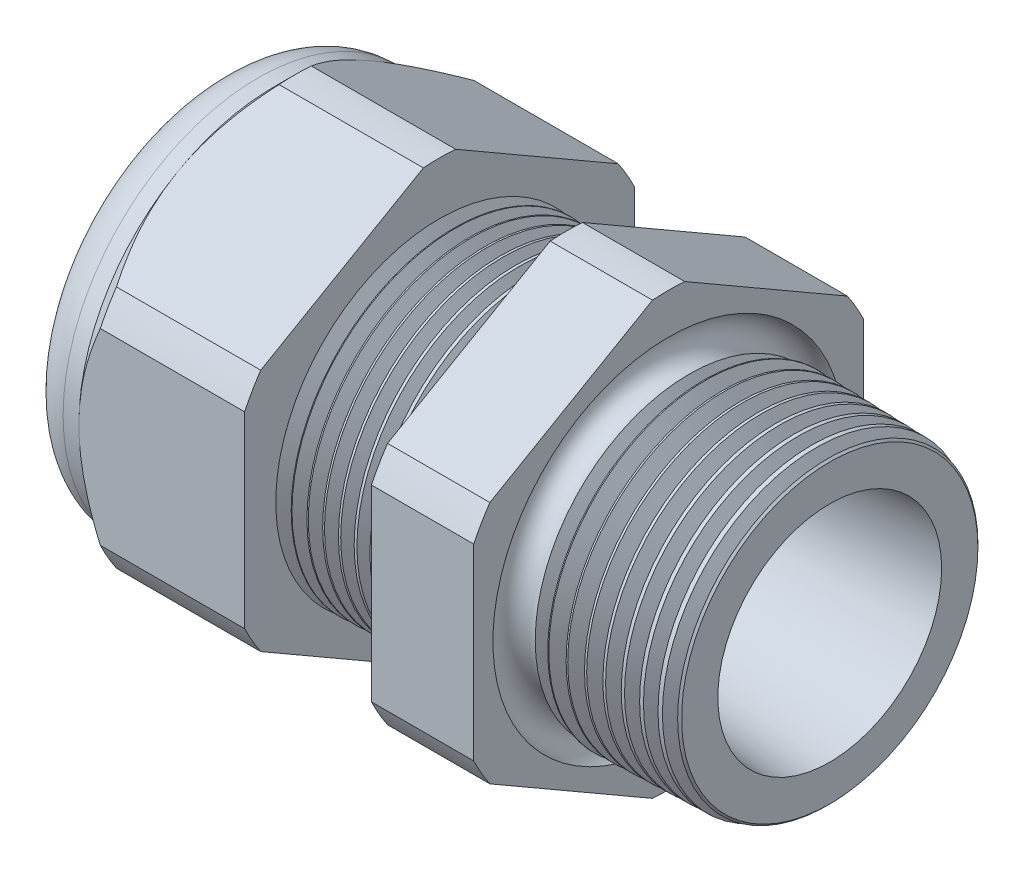
SolidWorks part; units mm, degrees
ref_plane "Front Plane" through (0, 0, 0) normal (0, 0, 1) x (1, 0, 0)
ref_plane "Top Plane" through (0, 0, 0) normal (0, 1, 0) x (1, 0, 0)
ref_plane "Right Plane" through (0, 0, 0) normal (1, 0, 0) x (0, 0, -1)
sketch "Sketch10" plane through (0, 0, 0) normal (0, 0, 1) x (1, 0, 0)
  line L0 (0, 0) -> (-115.3565, 0) construction
  line L1 (-29.972, 3.937) -> (-19.072, 3.937)
  line L2 (0, 5.4696) -> (0, 7.5016)
  line L3 (-7.874, 7.7078) -> (0, 7.5016)
  line L4 (-7.874, 19.05) -> (-7.874, 7.7078)
  line L5 (-7.874, 19.05) -> (-12.874, 19.05)
  line L6 (-12.874, 19.05) -> (-12.874, 7.8387)
  line L7 (-19.072, 8.001) -> (-12.874, 7.8387)
  line L8 (-19.072, 8.001) -> (-19.072, 19.05)
  line L9 (-19.072, 19.05) -> (-27.172, 19.05)
  line L10 (-27.172, 19.05) -> (-27.172, 9.525)
  line L11 (-27.172, 9.525) -> (-29.972, 9.525)
  line L12 (-29.972, 9.525) -> (-29.972, 3.937)
  line L13 (-19.072, 3.937) -> (0, 5.4696)
  dimension "D1" = 29.972
  dimension "D2" = 7.874
  dimension "D3" = 1.5
  dimension "D4" = 2.032
  dimension "A" = 16.002
  dimension "D6" = 19.05
  dimension "D8" = 38.1
  dimension "D9" = 2.8
  dimension "D10" = 8.1
  dimension "D11" = 5
  dimension "D" = 7.874
revolve "Revolve2" add sketch "Sketch10" angle 360 about L0
sketch "Sketch12" plane through (-27.172, 0, 0) normal (-1, 0, 0) x (0, 0, 1)
  line L1 (-0.7885, 10.5433) -> (-8.7365, 5.9545)
  line L2 (-9.525, 4.5888) -> (-9.525, -4.5888)
  line L3 (-8.7365, -5.9545) -> (-0.7885, -10.5433)
  line L4 (0.7885, -10.5433) -> (8.7365, -5.9545)
  line L5 (9.525, -4.5888) -> (9.525, 4.5888)
  line L6 (8.7365, 5.9545) -> (0.7885, 10.5433)
  circle A0 centre (0, 0) radius 9.525 construction
  arc A1 (0.7885, 10.5433) -> (-0.7885, 10.5433) centre (0, 0) ccw
  arc A2 (-8.7365, 5.9545) -> (-9.525, 4.5888) centre (0, 0) ccw
  arc A3 (-9.525, -4.5888) -> (-8.7365, -5.9545) centre (0, 0) ccw
  arc A4 (-0.7885, -10.5433) -> (0.7885, -10.5433) centre (0, 0) ccw
  arc A5 (8.7365, -5.9545) -> (9.525, -4.5888) centre (0, 0) ccw
  arc A6 (9.525, 4.5888) -> (8.7365, 5.9545) centre (0, 0) ccw
  dimension "D2" = 21.1455
  dimension "D1" = 19.05
extrude "Cut-Extrude2" cut sketch "Sketch12" against normal through all flip side to cut
fillet "Fillet4" radius 2.032 1 edges at (-29.972, 0, -9.525)
sketch "Sketch19" plane through (-27.172, 0, 0) normal (-1, 0, 0) x (0, 0, 1)
  line L0 (9.525, 0) -> (9.525, 4.5888) construction
  circle A0 centre (0, 0) radius 9.525
extrude "Cut-Extrude3" cut sketch "Sketch19" against normal blind 2 draft 45 flip side to cut
chamfer "Chamfer1" distance 0.254 angle 45 1 edges at (0, 0, -7.5016)
sketch "Sketch21" plane through (-29.972, 0, 0) normal (-1, 0, 0) x (0, 0, 1)
  circle A0 centre (0, 0) radius 3.937
  circle A2 centre (0, 0) radius 3.937 construction
extrude "plug" add sketch "Sketch21" against normal blind 3.81 separate body
sketch "Sketch22" plane through (-29.972, 0, 0) normal (-1, 0, 0) x (0, 0, 1)
  circle A0 centre (0, 0) radius 3.683
  circle A1 centre (0, 0) radius 3.937 construction
  dimension "D1" = 0.254
extrude "Cut-Extrude4" cut sketch "Sketch22" against normal blind 0.508
sketch "Sketch27" plane through (-29.464, 0, 0) normal (-1, 0, 0) x (0, 0, 1)
  line L0 (-4.3624, 0) -> (4.3624, 0) construction
  circle A0 centre (-2.1529, 0) radius 1.524
  circle A1 centre (0, 0) radius 3.683 construction
  dimension "D1" = 0.0061
  dimension "holedia" = 3.048
extrude "plugholes" cut sketch "Sketch27" against normal through all
pattern_circular "CirPattern1" count 2 over 360 about axis through (0, 0, 0) along (1, 0, 0) of "plugholes"
sketch "Sketch28" [suppressed] plane through (-29.464, 0, 0) normal (-1, 0, 0) x (0, 0, 1)
  circle A0 centre (0, 0) radius 0.762
  dimension "midholedia" = 3.048
extrude "midhole" [suppressed] cut sketch "Sketch28" against normal through all
sketch "Sketch29" plane through (0, 0, 0) normal (0, 0, 1) x (1, 0, 0)
  line L0 (-19.072, 8.001) -> (-18.339, 7.9818)
  line L1 (-12.874, 7.8387) -> (-19.072, 8.001) construction
  line L2 (-18.339, 7.9818) -> (-18.7221, 7.3566)
  line L3 (-18.7221, 7.3566) -> (-19.072, 8.001)
  dimension "D1" = 60
  dimension "D2" = 60
  dimension "D3" = 0.635
revolve "Cut-Revolve1" cut sketch "Sketch29" angle 360 about axis through (0, 0, 0) along (-1, 0, 0)
pattern_linear "LPattern1" count 8 spacing 0.762 along (1, 0, 0) of "Cut-Revolve1"
sketch "Sketch30" plane through (0, 0, 0) normal (0, 0, 1) x (1, 0, 0)
  line L0 (-7.874, 7.7078) -> (-6.9944, 7.6847)
  line L1 (-7.874, 10.5433) -> (-7.874, 5.9545) construction
  line L2 (-0.2539, 7.5082) -> (-7.874, 7.7078) construction
  line L3 (-6.9944, 7.6847) -> (-7.4542, 6.9345)
  line L4 (-7.4542, 6.9345) -> (-7.874, 7.7078)
  dimension "D1" = 60
  dimension "D2" = 60
  dimension "D3" = 0.762
revolve "Cut-Revolve2" cut sketch "Sketch30" angle 360 about axis through (0, 0, 0) along (-1, 0, 0)
pattern_linear "LPattern2" count 9 spacing 0.889 along (1, 0, 0) of "Cut-Revolve2"
sketch "Sketch31" [suppressed] plane through (-38.354, 0, 0) normal (-1, 0, 0) x (0, 0, 1)
  line L0 (-1.905, 1.905) -> (1.905, 1.905)
  line L1 (-1.905, -1.905) -> (1.905, -1.905)
  circle A0 centre (0, 0) radius 1.905 construction
  arc A1 (-1.905, 1.905) -> (-1.905, -1.905) centre (-1.905, 0) ccw
  arc A2 (1.905, 1.905) -> (1.905, -1.905) centre (1.905, 0) cw
extrude "Cut-Extrude5" [suppressed] cut sketch "Sketch31" against normal through all
sketch "Sketch32" plane through (0, 0, 0) normal (0, 0, 1) x (1, 0, 0)
  line L0 (-7.874, 10.5433) -> (-7.874, 5.9545) construction
  circle A0 centre (-7.747, 7.7078) radius 0.889
  dimension "D2" = 1.778
  dimension "D1" = 0.127
revolve "Cut-Revolve3" cut sketch "Sketch32" angle 360 about axis through (0, 0, 0) along (-1, 0, 0)
